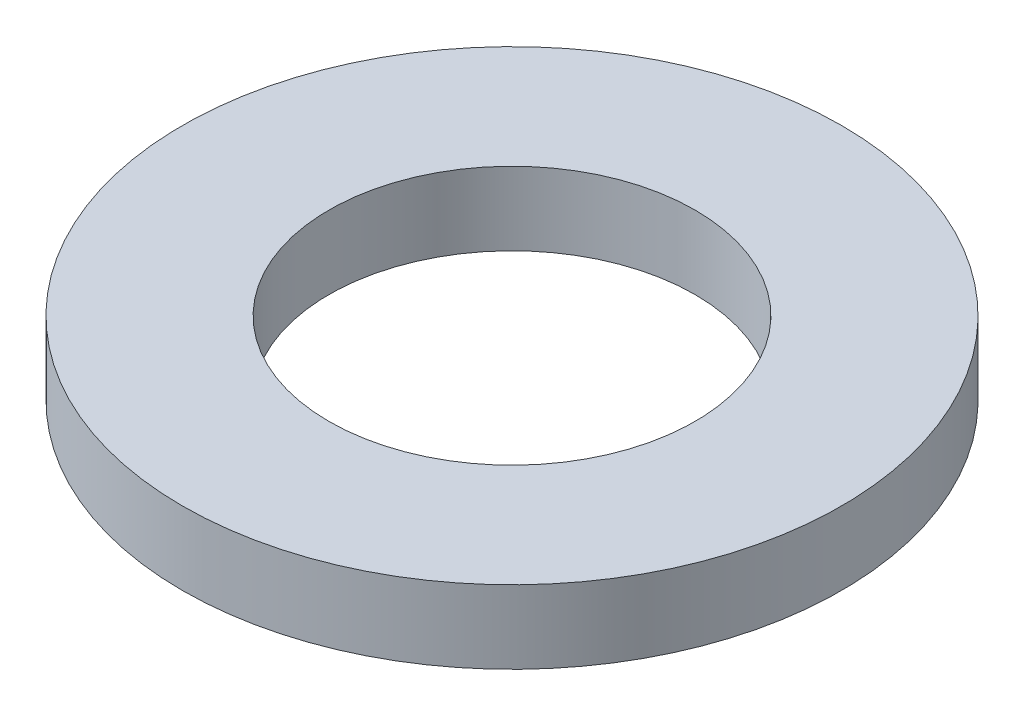
SolidWorks part; units mm, degrees
material "AISI 304"
ref_plane "前视基准面" through (0, 0, 0) normal (0, 0, 1) x (1, 0, 0)
ref_plane "上视基准面" through (0, 0, 0) normal (0, 1, 0) x (1, 0, 0)
ref_plane "右视基准面" through (0, 0, 0) normal (1, 0, 0) x (0, 0, -1)
sketch "草图1" plane through (0, 0, 0) normal (0, 1, 0) x (1, 0, 0)
  circle A0 centre (0, 0) radius 2.5
  circle A1 centre (0, 0) radius 4.5
  dimension "D1" = 5
  dimension "D2" = 9
extrude "凸台-拉伸1" add sketch "草图1" along normal blind 1
